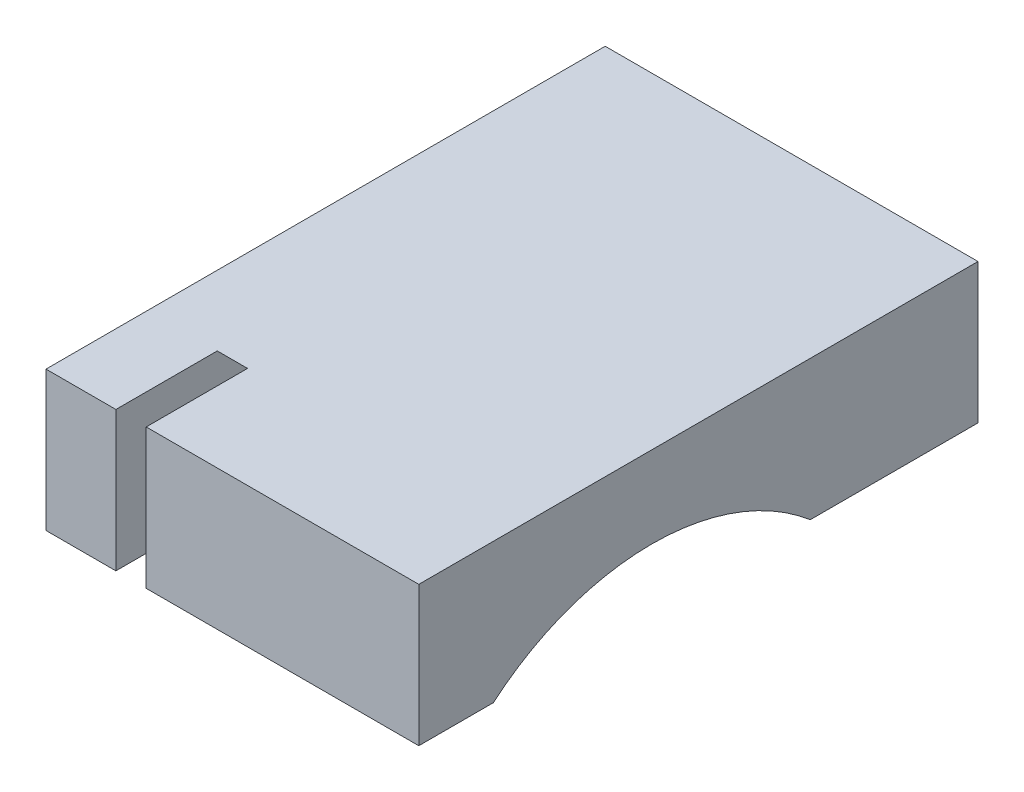
SolidWorks part; units mm, degrees
ref_plane "Спереди" through (0, 0, 0) normal (0, 0, 1) x (1, 0, 0)
ref_plane "Сверху" through (0, 0, 0) normal (0, 1, 0) x (1, 0, 0)
ref_plane "Справа" through (0, 0, 0) normal (1, 0, 0) x (0, 0, -1)
sketch "Эскиз1" plane through (0, 0, 0) normal (1, 0, 0) x (0, 0, -1)
  line L1 (0, 0) -> (24, 0)
  line L2 (0, 0) -> (0, 6)
  line L3 (0, 6) -> (24, 6)
  line L4 (24, 0) -> (24, 6)
  dimension "D1" = 24
  dimension "D2" = 6
extrude "Бобышка-Вытянуть1" add sketch "Эскиз1" along normal blind 16
sketch "Эскиз2" plane through (16, 0, 0) normal (1, 0, 0) x (0, 0, -1)
  line L0 (0, 0) -> (24, 0) construction
  line L1 (0, 6) -> (0, 0) construction
  arc A0 (3.1993, 0) -> (16.8007, 0) centre (10, -8) cw
  line M2 (0, 0) -> (24, 0)
  dimension "D1" = 10.5
  dimension "D2" = 8
  dimension "D3" = 10
extrude "Вырез-Вытянуть1" cut sketch "Эскиз2" against normal blind 13 contours A0 M2
sketch "Эскиз3" plane through (16, 0, 0) normal (1, 0, 0) x (0, 0, -1)
  line L0 (4.3507, 6) -> (11.8715, 2.3319)
  line L1 (24, 6) -> (0, 6) construction
  arc A0 (16.8007, 0) -> (3.1993, 0) centre (10, -8) ccw construction
  arc M1 (3.1993, 0) -> (16.8007, 0) centre (10, -8) cw
  line M4 (24, 6) -> (0, 6)
  line M5 (0, 6) -> (0, 0)
  line M6 (0, 0) -> (3.1993, 0)
  dimension "D1" = 26
  dimension "D2" = 7.3
extrude "Вырез-Вытянуть6" cut sketch "Эскиз3" against normal up to surface (1.3 mm away) from offset 11.7 contours L0 M4 M5 M6 M1 up to face at (3, 1.25, -10)
